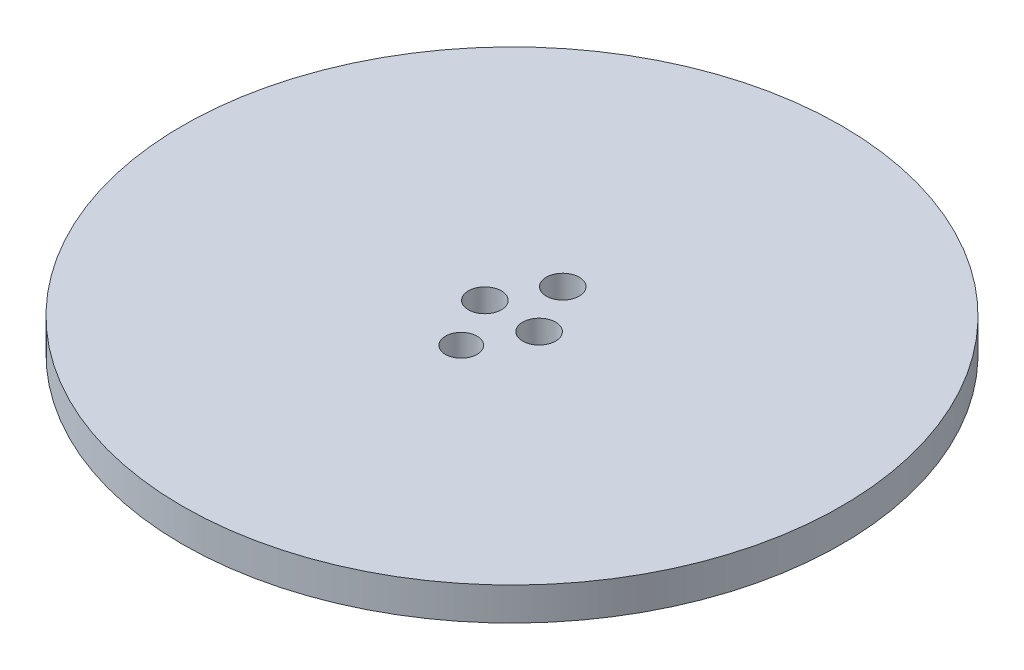
SolidWorks part; units mm, degrees
ref_plane "Front Plane" through (0, 0, 0) normal (0, 0, 1) x (1, 0, 0)
ref_plane "Top Plane" through (0, 0, 0) normal (0, 1, 0) x (1, 0, 0)
ref_plane "Right Plane" through (0, 0, 0) normal (1, 0, 0) x (0, 0, -1)
sketch "Sketch1" plane through (0, 0, 0) normal (0, 1, 0) x (1, 0, 0)
  circle A0 centre (0, 0) radius 15.875
  dimension "D1" = 31.75
extrude "Boss-Extrude1" add sketch "Sketch1" along normal blind 6.35
sketch "Sketch2" plane through (0, 6.35, 0) normal (0, 1, 0) x (1, 0, 0)
  circle A0 centre (0, 0) radius 63.5
  dimension "D1" = 127
extrude "Boss-Extrude2" add sketch "Sketch2" along normal blind 6.35
sketch "Sketch5" plane through (0, 12.7, 0) normal (0, 1, 0) x (1, 0, 0)
  line L0 (-5.3935, -5.3828) -> (0, 0)
  line L1 (0, 0) -> (7.62, -0.0076)
  arc A0 (7.62, -0.0076) -> (-5.3935, -5.3828) centre (0, 0) ccw
extrude "Boss-Extrude4" [suppressed] add sketch "Sketch5" along normal blind 12.7
sketch "Sketch6" plane through (0, 12.7, 0) normal (0, 1, 0) x (1, 0, 0)
  circle A0 centre (1.823, -4.2085) radius 2.4637
extrude "Boss-Extrude5" [suppressed] add sketch "Sketch6" along normal blind 12.7
sketch "Sketch7" [suppressed] plane through (0, 25.4, 0) normal (0, 1, 0) x (1, 0, 0)
  circle A0 centre (0, 0) radius 63.5
extrude "Boss-Extrude6" [suppressed] add sketch "Sketch7" along normal blind 5.08
sketch "Sketch9" plane through (0, 0, 0) normal (0, -1, 0) x (1, 0, 0)
  circle A0 centre (0, 9.779) radius 3.048
  dimension "D1" = 9.779
extrude "Cut-Extrude1" cut sketch "Sketch9" against normal through all
sketch "Sketch10" plane through (0, 0, 0) normal (0, -1, 0) x (1, 0, 0)
  circle A0 centre (0, -9.779) radius 3.175
  dimension "D1" = 9.779
extrude "Cut-Extrude2" cut sketch "Sketch10" against normal blind 12.7
sketch "Sketch11" plane through (0, 0, 0) normal (0, -1, 0) x (1, 0, 0)
  circle A0 centre (-5.2248, 0) radius 3.175
  dimension "D1" = 5.2248
extrude "Cut-Extrude3" cut sketch "Sketch11" against normal blind 12.7
sketch "Sketch12" plane through (0, 0, 0) normal (0, -1, 0) x (1, 0, 0)
  circle A0 centre (5.2248, 0) radius 3.175
  dimension "D1" = 5.2248
extrude "Cut-Extrude4" cut sketch "Sketch12" against normal blind 12.7
